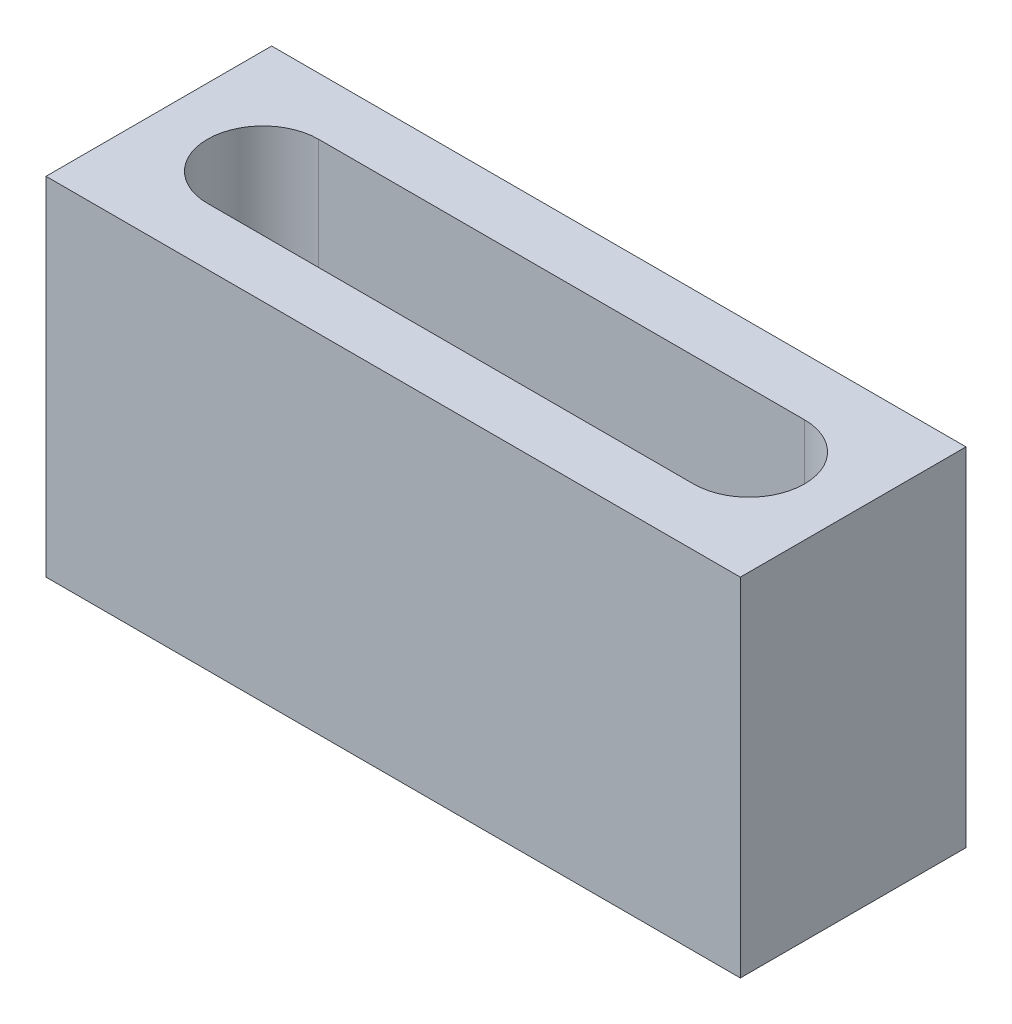
SolidWorks part; units mm, degrees
ref_plane "Front Plane" through (0, 0, 0) normal (0, 0, 1) x (1, 0, 0)
ref_plane "Top Plane" through (0, 0, 0) normal (0, 1, 0) x (1, 0, 0)
ref_plane "Right Plane" through (0, 0, 0) normal (1, 0, 0) x (0, 0, -1)
sketch "Sketch1" plane through (0, 0, 0) normal (0, 1, 0) x (1, 0, 0)
  line L0 (-10, 0) -> (-7, 0) construction
  line L1 (-10, 3.25) -> (10, 3.25)
  line L2 (-10, 3.25) -> (-10, -3.25)
  line L3 (-10, -3.25) -> (10, -3.25)
  line L4 (10, 3.25) -> (10, -3.25)
  line L5 (-10, 3.25) -> (10, -3.25) construction
  line L6 (-10, -3.25) -> (10, 3.25) construction
  line L7 (10, 0) -> (7, 0) construction
  line L8 (-7, 0) -> (7, 0) construction
  line L11 (-7, 1.6) -> (7, 1.6)
  line L12 (-7, -1.6) -> (7, -1.6)
  arc A2 (-7, 1.6) -> (-7, -1.6) centre (-7, 0) ccw
  arc A3 (7, -1.6) -> (7, 1.6) centre (7, 0) ccw
  point P0 (0, 0)
  point P10 (0, 0)
  dimension "D1" = 6.5
  dimension "D2" = 20
extrude "Boss-Extrude1" add sketch "Sketch1" along normal blind 10
